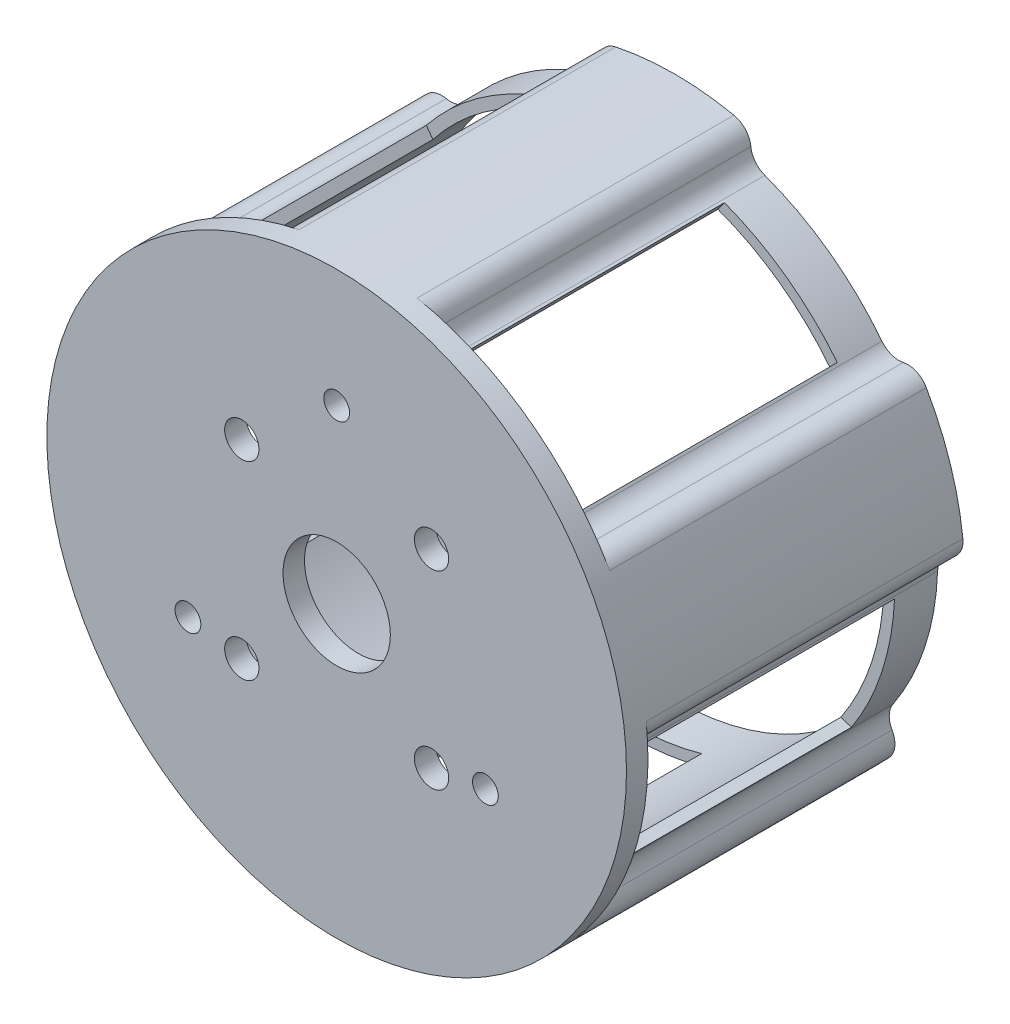
SolidWorks part; units mm, degrees
ref_plane "前视基准面" through (0, 0, 0) normal (0, 0, 1) x (1, 0, 0)
ref_plane "上视基准面" through (0, 0, 0) normal (0, 1, 0) x (1, 0, 0)
ref_plane "右视基准面" through (0, 0, 0) normal (1, 0, 0) x (0, 0, -1)
sketch "草图1" plane through (0, 0, 0) normal (0, 0, 1) x (1, 0, 0)
  circle A0 centre (0, 0) radius 23.5
  circle A1 centre (0, 0) radius 27
  circle A2 centre (0, 25) radius 1
  circle A3 centre (23.7764, 7.7254) radius 1
  circle A4 centre (14.6946, -20.2254) radius 1
  circle A5 centre (-14.6946, -20.2254) radius 1
  circle A6 centre (-23.7764, 7.7254) radius 1
  point P16 (0, 0)
extrude "凸台-拉伸1" add sketch "草图1" along normal blind 27.5
sketch "草图2" plane through (0, 0, 27.5) normal (0, 0, 1) x (1, 0, 0)
  line L0 (-19.4693, -13.1605) -> (-22.9147, -14.2799)
  line L1 (6.5, -22.5832) -> (6.5, -26.2059)
  line L2 (-23.4865, -0.7967) -> (-26.9319, -1.9162)
  line L3 (-6.5, -22.5832) -> (-6.5, -26.2059)
  line L4 (-18.5327, 14.4496) -> (-20.6621, 17.3804)
  line L5 (-8.0154, 22.0908) -> (-10.1448, 25.0216)
  line L6 (8.0154, 22.0908) -> (10.1448, 25.0216)
  line L7 (18.5327, 14.4496) -> (20.6621, 17.3804)
  line L8 (23.4865, -0.7967) -> (26.9319, -1.9162)
  line L9 (19.4693, -13.1605) -> (22.9147, -14.2799)
  circle A0 centre (0, 0) radius 27 construction
  circle A1 centre (0, 0) radius 23.5 construction
  arc A2 (-6.5, -22.5832) -> (6.5, -22.5832) centre (0, 0) ccw
  arc A3 (-6.5, -26.2059) -> (6.5, -26.2059) centre (0, 0) ccw
  arc A4 (-26.9319, -1.9162) -> (-22.9147, -14.2799) centre (0, 0) ccw
  arc A5 (-23.4865, -0.7967) -> (-19.4693, -13.1605) centre (0, 0) ccw
  arc A6 (-10.1448, 25.0216) -> (-20.6621, 17.3804) centre (0, 0) ccw
  arc A7 (-8.0154, 22.0908) -> (-18.5327, 14.4496) centre (0, 0) ccw
  arc A8 (20.6621, 17.3804) -> (10.1448, 25.0216) centre (0, 0) ccw
  arc A9 (18.5327, 14.4496) -> (8.0154, 22.0908) centre (0, 0) ccw
  arc A10 (22.9147, -14.2799) -> (26.9319, -1.9162) centre (0, 0) ccw
  arc A11 (19.4693, -13.1605) -> (23.4865, -0.7967) centre (0, 0) ccw
  point P28 (0, 0)
extrude "切除-拉伸1" cut sketch "草图2" against normal blind 26
sketch "草图3" plane through (0, 0, 27.5) normal (0, 0, 1) x (1, 0, 0)
  circle A0 centre (0, 0) radius 27
  circle A1 centre (8.8388, 8.8388) radius 1.5957
  circle A2 centre (-8.8388, 8.8388) radius 1.5957
  circle A3 centre (-8.8388, -8.8388) radius 1.5957
  circle A11 centre (8.8388, -8.8388) radius 1.5957
extrude "凸台-拉伸2" add sketch "草图3" along normal blind 1.5
sketch "草图4" plane through (0, 0, 29) normal (0, 0, 1) x (1, 0, 0)
  circle A0 centre (0, 0) radius 5
extrude "切除-拉伸2" cut sketch "草图4" against normal blind 1.5
sketch "草图5" plane through (0, 0, 29) normal (0, 0, 1) x (1, 0, 0)
  circle A0 centre (0, 16) radius 1.2
  circle A1 centre (13.8564, -8) radius 1.2
  circle A2 centre (-13.8564, -8) radius 1.2
  point P11 (0, 0)
extrude "切除-拉伸3" cut sketch "草图5" against normal blind 1.5
sketch "草图6" plane through (0, 0, 0) normal (0, 0, -1) x (-1, 0, 0)
  circle A0 centre (23.7764, 7.7254) radius 1 construction
  circle A1 centre (0, 0) radius 27
  circle A2 centre (0, 0) radius 27
  circle A3 centre (0, 25) radius 1 construction
  circle A4 centre (-23.7764, 7.7254) radius 1 construction
  circle A5 centre (-14.6946, -20.2254) radius 1 construction
  circle A6 centre (14.6946, -20.2254) radius 1 construction
  circle A7 centre (0, 0) radius 23.5 construction
  circle A8 centre (0, 0) radius 23.5
  circle A9 centre (14.6946, -20.2254) radius 1
  circle A10 centre (-14.6946, -20.2254) radius 1
  circle A11 centre (-23.7764, 7.7254) radius 1
  circle A12 centre (0, 25) radius 1
  circle A13 centre (23.7764, 7.7254) radius 1
  dimension "D1" = 0
extrude "凸台-拉伸3" add sketch "草图6" along normal blind 2
sketch "草图7" plane through (0, 0, 29) normal (0, 0, 1) x (1, 0, 0)
  circle A0 centre (8.8388, 8.8388) radius 1.5957 construction
  circle A1 centre (0, 0) radius 27
  circle A2 centre (0, 0) radius 27
  circle A3 centre (0, 0) radius 5 construction
  circle A4 centre (8.8388, -8.8388) radius 1.5957 construction
  circle A5 centre (13.8564, -8) radius 1.2 construction
  circle A6 centre (-8.8388, -8.8388) radius 1.5957 construction
  circle A7 centre (-13.8564, -8) radius 1.2 construction
  circle A8 centre (-8.8388, 8.8388) radius 1.5957 construction
  circle A9 centre (0, 16) radius 1.2 construction
  circle A10 centre (0, 16) radius 1.2
  circle A11 centre (-8.8388, 8.8388) radius 1.5957
  circle A12 centre (-13.8564, -8) radius 1.2
  circle A13 centre (-8.8388, -8.8388) radius 1.5957
  circle A14 centre (13.8564, -8) radius 1.2
  circle A15 centre (8.8388, -8.8388) radius 1.5957
  circle A16 centre (0, 0) radius 5
  circle A17 centre (8.8388, 8.8388) radius 1.5957
  dimension "D1" = 0
extrude "凸台-拉伸4" add sketch "草图7" along normal blind 0.5
fillet "圆角1" radius 1 1 edges at (-21.192, -13.7202, 27.5)
fillet "圆角2" radius 1 1 edges at (-25.2092, -1.3565, 27.5)
fillet "圆角3" radius 1 8 edges at (-6.5, -24.3945, 27.5) (6.5, -24.3945, 27.5) (21.192, -13.7202, 27.5) (25.2092, -1.3565, 27.5) (19.5974, 15.915, 27.5) (9.0801, 23.5562, 27.5) (-9.0801, 23.5562, 27.5) (-19.5974, 15.915, 27.5)
sketch "草图8" plane through (0, 0, 1.5) normal (0, 0, 1) x (1, 0, 0)
  line L0 (19.4693, -13.1605) -> (22.9147, -14.2799)
  line L1 (26.9319, -1.9162) -> (23.4865, -0.7967)
  line L2 (10.1448, 25.0216) -> (8.0154, 22.0908)
  line L3 (18.5327, 14.4496) -> (20.6621, 17.3804)
  line L4 (10.1448, 25.0216) -> (8.0154, 22.0908)
  line L5 (18.5327, 14.4496) -> (20.6621, 17.3804)
  line L6 (-6.5, -22.5832) -> (-6.5, -26.2059)
  line L7 (6.5, -26.2059) -> (6.5, -22.5832)
  line L8 (-23.4865, -0.7967) -> (-26.9319, -1.9162)
  line L9 (-22.9147, -14.2799) -> (-19.4693, -13.1605)
  line L10 (-8.0154, 22.0908) -> (-10.1448, 25.0216)
  line L11 (-20.6621, 17.3804) -> (-18.5327, 14.4496)
  arc A0 (19.4693, -13.1605) -> (23.4865, -0.7967) centre (0, 0) ccw
  arc A1 (22.9147, -14.2799) -> (26.9319, -1.9162) centre (0, 0) ccw
  arc A2 (20.6621, 17.3804) -> (10.1448, 25.0216) centre (0, 0) ccw
  arc A3 (18.5327, 14.4496) -> (8.0154, 22.0908) centre (0, 0) ccw
  arc A4 (20.6621, 17.3804) -> (10.1448, 25.0216) centre (0, 0) ccw
  arc A5 (18.5327, 14.4496) -> (8.0154, 22.0908) centre (0, 0) ccw
  arc A6 (-6.5, -22.5832) -> (6.5, -22.5832) centre (0, 0) ccw
  arc A7 (-6.5, -26.2059) -> (6.5, -26.2059) centre (0, 0) ccw
  arc A8 (-23.4865, -0.7967) -> (-19.4693, -13.1605) centre (0, 0) ccw
  arc A9 (-26.9319, -1.9162) -> (-22.9147, -14.2799) centre (0, 0) ccw
  arc A10 (-8.0154, 22.0908) -> (-18.5327, 14.4496) centre (0, 0) ccw
  arc A11 (-10.1448, 25.0216) -> (-20.6621, 17.3804) centre (0, 0) ccw
  point P25 (0, 0)
  dimension "D1" = 0
extrude "切除-拉伸4" cut sketch "草图8" against normal blind 0.8
fillet "圆角4" radius 1 10 edges at (21.192, -13.7202, 0.7) (25.2092, -1.3565, 0.7) (9.0801, 23.5562, 0.7) (-9.0801, 23.5562, 0.7) (-19.5974, 15.915, 0.7) (19.5974, 15.915, 0.7) (-25.2092, -1.3565, 0.7) (-21.192, -13.7202, 0.7) (-6.5, -24.3945, 0.7) (6.5, -24.3945, 0.7)
sketch "草图9" plane through (0, 0, -2) normal (0, 0, -1) x (-1, 0, 0)
  line L0 (21.1533, 14.3366) -> (20.0835, 14.0322)
  arc A1 (-11.0809, -24.6214) -> (-8.7753, -24.1375) centre (-10.2601, -22.7976) ccw
  arc A2 (-6.7402, -23.5546) -> (-8.7753, -24.1375) centre (-7.2905, -25.4774) ccw
  arc A3 (-6.7402, -23.5546) -> (6.7402, -23.5546) centre (0, 0) ccw
  arc A4 (8.7753, -24.1375) -> (6.7402, -23.5546) centre (7.2905, -25.4774) ccw
  arc A5 (8.7753, -24.1375) -> (11.0809, -24.6214) centre (10.2601, -22.7976) ccw
  arc A7 (19.9922, -18.147) -> (20.2444, -15.8047) centre (18.5113, -16.8027) ccw
  arc A8 (20.3189, -13.6891) -> (20.2444, -15.8047) centre (21.9776, -14.8066) ccw
  arc A9 (20.3189, -13.6891) -> (24.4846, -0.8684) centre (0, 0) ccw
  arc A10 (25.6678, 0.8869) -> (24.4846, -0.8684) centre (26.4833, -0.9393) ccw
  arc A11 (25.6678, 0.8869) -> (26.8405, 2.9301) centre (24.8524, 2.7131) ccw
  arc A13 (23.4367, 13.406) -> (21.1533, 14.3366) centre (21.7007, 12.4129) ccw
  arc A14 (20.0835, 14.0322) -> (8.3921, 23.0179) centre (0, 0) ccw
  arc A15 (7.0883, 24.6856) -> (8.3921, 23.0179) centre (9.0772, 24.8969) ccw
  arc A16 (7.0883, 24.6856) -> (5.5075, 26.4323) centre (5.0995, 24.4744) ccw
  arc A18 (-5.5075, 26.4323) -> (-7.0883, 24.6856) centre (-5.0995, 24.4744) ccw
  arc A19 (-8.3921, 23.0179) -> (-7.0883, 24.6856) centre (-9.0772, 24.8969) ccw
  arc A20 (-8.3921, 23.0179) -> (-19.298, 15.0943) centre (0, 0) ccw
  arc A21 (-21.287, 14.3697) -> (-19.298, 15.0943) centre (-20.8734, 16.3265) ccw
  arc A22 (-21.287, 14.3697) -> (-23.4367, 13.406) centre (-21.7007, 12.4129) ccw
  arc A24 (-26.8405, 2.9301) -> (-25.6678, 0.8869) centre (-24.8524, 2.7131) ccw
  arc A25 (-24.4846, -0.8684) -> (-25.6678, 0.8869) centre (-26.4833, -0.9393) ccw
  arc A26 (-24.4846, -0.8684) -> (-20.3189, -13.6891) centre (0, 0) ccw
  arc A27 (-20.2444, -15.8047) -> (-20.3189, -13.6891) centre (-21.9776, -14.8066) ccw
  arc A28 (-20.2444, -15.8047) -> (-19.9922, -18.147) centre (-18.5113, -16.8027) ccw
  arc A29 (-11.0809, -24.6214) -> (11.0809, -24.6214) centre (0, 0) ccw
  arc A30 (19.9922, -18.147) -> (26.8405, 2.9301) centre (0, 0) ccw
  arc A31 (23.4367, 13.406) -> (5.5075, 26.4323) centre (0, 0) ccw
  arc A32 (-5.5075, 26.4323) -> (-23.4367, 13.406) centre (0, 0) ccw
  arc A33 (-26.8405, 2.9301) -> (-19.9922, -18.147) centre (0, 0) ccw
extrude "切除-拉伸5" cut sketch "草图9" against normal up to surface (29.5 mm away) up to face at (1.2, 16, 27.5)
fillet "圆角5" radius 2 1 edges at (-20.0835, 14.0322, 12.75)
sketch "草图10" plane through (0, 0, -2) normal (0, 0, -1) x (-1, 0, 0)
  circle A0 centre (0, 0) radius 23.5 construction
  circle A1 centre (0, 0) radius 23.5
  circle A2 centre (14.6946, -20.2254) radius 1 construction
  circle A3 centre (23.7764, 7.7254) radius 1 construction
  circle A4 centre (0, 25) radius 1 construction
  circle A5 centre (-23.7764, 7.7254) radius 1 construction
  circle A6 centre (-14.6946, -20.2254) radius 1 construction
  circle A7 centre (-14.6946, -20.2254) radius 1
  circle A8 centre (-23.7764, 7.7254) radius 1
  circle A9 centre (0, 25) radius 1
  circle A10 centre (23.7764, 7.7254) radius 1
  circle A11 centre (14.6946, -20.2254) radius 1
  arc A30 (-21.287, 14.3697) -> (-23.4367, 13.406) centre (-21.7007, 12.4129) ccw
  arc A31 (-23.4367, 13.406) -> (-26.8405, 2.9301) centre (0, 0) ccw
  arc A32 (-26.8405, 2.9301) -> (-25.6678, 0.8869) centre (-24.8524, 2.7131) ccw
  arc A33 (-24.4846, -0.8684) -> (-25.6678, 0.8869) centre (-26.4833, -0.9393) ccw
  arc A34 (-24.4846, -0.8684) -> (-20.3189, -13.6891) centre (0, 0) ccw
  arc A35 (-20.2444, -15.8047) -> (-20.3189, -13.6891) centre (-21.9776, -14.8066) ccw
  arc A36 (-20.2444, -15.8047) -> (-19.9922, -18.147) centre (-18.5113, -16.8027) ccw
  arc A37 (-19.9922, -18.147) -> (-11.0809, -24.6214) centre (0, 0) ccw
  arc A38 (-11.0809, -24.6214) -> (-8.7753, -24.1375) centre (-10.2601, -22.7976) ccw
  arc A39 (-6.7402, -23.5546) -> (-8.7753, -24.1375) centre (-7.2905, -25.4774) ccw
  arc A40 (-6.7402, -23.5546) -> (6.7402, -23.5546) centre (0, 0) ccw
  arc A41 (8.7753, -24.1375) -> (6.7402, -23.5546) centre (7.2905, -25.4774) ccw
  arc A42 (8.7753, -24.1375) -> (11.0809, -24.6214) centre (10.2601, -22.7976) ccw
  arc A43 (11.0809, -24.6214) -> (19.9922, -18.147) centre (0, 0) ccw
  arc A44 (19.9922, -18.147) -> (20.2444, -15.8047) centre (18.5113, -16.8027) ccw
  arc A45 (20.3189, -13.6891) -> (20.2444, -15.8047) centre (21.9776, -14.8066) ccw
  arc A46 (20.3189, -13.6891) -> (24.4846, -0.8684) centre (0, 0) ccw
  arc A47 (25.6678, 0.8869) -> (24.4846, -0.8684) centre (26.4833, -0.9393) ccw
  arc A48 (25.6678, 0.8869) -> (26.8405, 2.9301) centre (24.8524, 2.7131) ccw
  arc A49 (26.8405, 2.9301) -> (23.4367, 13.406) centre (0, 0) ccw
  arc A50 (23.4367, 13.406) -> (21.287, 14.3697) centre (21.7007, 12.4129) ccw
  arc A51 (19.298, 15.0943) -> (21.287, 14.3697) centre (20.8734, 16.3265) ccw
  arc A52 (19.298, 15.0943) -> (8.3921, 23.0179) centre (0, 0) ccw
  arc A53 (7.0883, 24.6856) -> (8.3921, 23.0179) centre (9.0772, 24.8969) ccw
  arc A54 (7.0883, 24.6856) -> (5.5075, 26.4323) centre (5.0995, 24.4744) ccw
  arc A55 (5.5075, 26.4323) -> (-5.5075, 26.4323) centre (0, 0) ccw
  arc A56 (-5.5075, 26.4323) -> (-7.0883, 24.6856) centre (-5.0995, 24.4744) ccw
  arc A57 (-8.3921, 23.0179) -> (-7.0883, 24.6856) centre (-9.0772, 24.8969) ccw
  arc A58 (-8.3921, 23.0179) -> (-19.298, 15.0943) centre (0, 0) ccw
  arc A59 (-21.287, 14.3697) -> (-19.298, 15.0943) centre (-20.8734, 16.3265) ccw
  arc A60 (-21.287, 14.3697) -> (-23.4367, 13.406) centre (-21.7007, 12.4129) ccw
  arc A61 (-23.4367, 13.406) -> (-26.8405, 2.9301) centre (0, 0) ccw
  arc A62 (-26.8405, 2.9301) -> (-25.6678, 0.8869) centre (-24.8524, 2.7131) ccw
  arc A63 (-24.4846, -0.8684) -> (-25.6678, 0.8869) centre (-26.4833, -0.9393) ccw
  arc A64 (-24.4846, -0.8684) -> (-20.3189, -13.6891) centre (0, 0) ccw
  arc A65 (-20.2444, -15.8047) -> (-20.3189, -13.6891) centre (-21.9776, -14.8066) ccw
  arc A66 (-20.2444, -15.8047) -> (-19.9922, -18.147) centre (-18.5113, -16.8027) ccw
  arc A67 (-19.9922, -18.147) -> (-11.0809, -24.6214) centre (0, 0) ccw
  arc A68 (-11.0809, -24.6214) -> (-8.7753, -24.1375) centre (-10.2601, -22.7976) ccw
  arc A69 (-6.7402, -23.5546) -> (-8.7753, -24.1375) centre (-7.2905, -25.4774) ccw
  arc A70 (-6.7402, -23.5546) -> (6.7402, -23.5546) centre (0, 0) ccw
  arc A71 (8.7753, -24.1375) -> (6.7402, -23.5546) centre (7.2905, -25.4774) ccw
  arc A72 (8.7753, -24.1375) -> (11.0809, -24.6214) centre (10.2601, -22.7976) ccw
  arc A73 (11.0809, -24.6214) -> (19.9922, -18.147) centre (0, 0) ccw
  arc A74 (19.9922, -18.147) -> (20.2444, -15.8047) centre (18.5113, -16.8027) ccw
  arc A75 (20.3189, -13.6891) -> (20.2444, -15.8047) centre (21.9776, -14.8066) ccw
  arc A76 (20.3189, -13.6891) -> (24.4846, -0.8684) centre (0, 0) ccw
  arc A77 (25.6678, 0.8869) -> (24.4846, -0.8684) centre (26.4833, -0.9393) ccw
  arc A78 (25.6678, 0.8869) -> (26.8405, 2.9301) centre (24.8524, 2.7131) ccw
  arc A79 (26.8405, 2.9301) -> (23.4367, 13.406) centre (0, 0) ccw
  arc A80 (23.4367, 13.406) -> (21.287, 14.3697) centre (21.7007, 12.4129) ccw
  arc A81 (19.298, 15.0943) -> (21.287, 14.3697) centre (20.8734, 16.3265) ccw
  arc A82 (19.298, 15.0943) -> (8.3921, 23.0179) centre (0, 0) ccw
  arc A83 (7.0883, 24.6856) -> (8.3921, 23.0179) centre (9.0772, 24.8969) ccw
  arc A84 (7.0883, 24.6856) -> (5.5075, 26.4323) centre (5.0995, 24.4744) ccw
  arc A85 (5.5075, 26.4323) -> (-5.5075, 26.4323) centre (0, 0) ccw
  arc A86 (-5.5075, 26.4323) -> (-7.0883, 24.6856) centre (-5.0995, 24.4744) ccw
  arc A87 (-8.3921, 23.0179) -> (-7.0883, 24.6856) centre (-9.0772, 24.8969) ccw
  arc A88 (-8.3921, 23.0179) -> (-19.298, 15.0943) centre (0, 0) ccw
  arc A89 (-21.287, 14.3697) -> (-19.298, 15.0943) centre (-20.8734, 16.3265) ccw
  dimension "D1" = 0
extrude "凸台-拉伸6" add sketch "草图10" against normal blind 4
